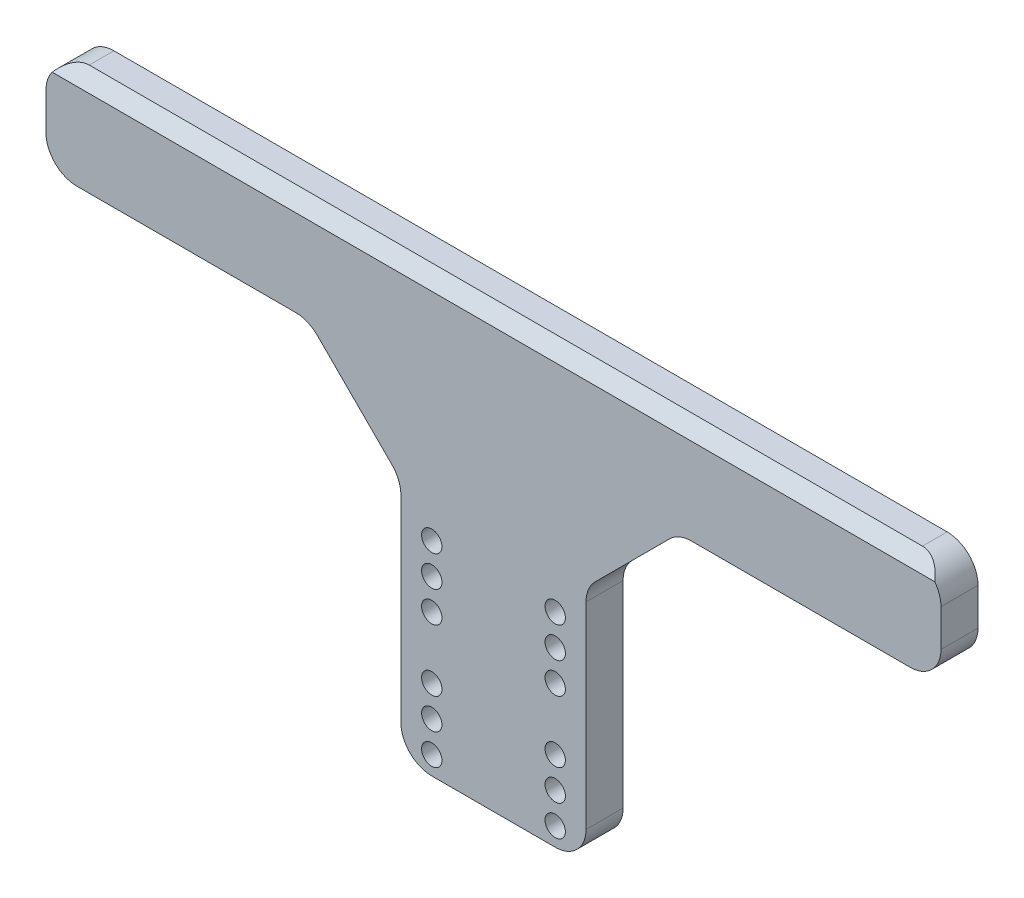
SolidWorks part; units mm, degrees
ref_plane "Front" through (0, 0, 0) normal (0, 0, 1) x (1, 0, 0)
ref_plane "Top" through (0, 0, 0) normal (0, 1, 0) x (1, 0, 0)
ref_plane "Right" through (0, 0, 0) normal (1, 0, 0) x (0, 0, -1)
sketch "Esquisse1" plane through (0, 0, 0) normal (0, 0, 1) x (1, 0, 0)
  line L1 (0, 0) -> (145, 0)
  line L2 (0, 0) -> (0, 40)
  line L3 (0, 40) -> (145, 40)
  line L4 (145, 0) -> (145, 40)
  dimension "D1" = 145
  dimension "D2" = 40
extrude "Boss.-Extru.1" add sketch "Esquisse1" along normal blind 6
sketch "Esquisse2" plane through (0, 0, 6) normal (0, 0, 1) x (1, 0, 0)
  line L0 (72.5, 0) -> (72.5, 40) construction
  line L1 (0, 0) -> (145, 0) construction
  line L2 (145, 40) -> (0, 40) construction
  line L3 (72.5, 13) -> (26.2893, 13) construction
  line L4 (62.5, 3) -> (62.5, 8) construction
  circle A0 centre (62.5, 23) radius 1.65
  circle A1 centre (62.5, 3) radius 1.65
  circle A2 centre (82.5, 3) radius 1.65
  circle A3 centre (82.5, 23) radius 1.65
  circle A4 centre (62.5, 28) radius 1.65
  circle A5 centre (62.5, 8) radius 1.65
  circle A6 centre (82.5, 8) radius 1.65
  circle A7 centre (82.5, 28) radius 1.65
  circle A8 centre (62.5, 33) radius 1.65
  circle A9 centre (62.5, 13) radius 1.65
  circle A10 centre (82.5, 13) radius 1.65
  circle A11 centre (82.5, 33) radius 1.65
  dimension "D1" = 20
  dimension "D2" = 20
  dimension "D3" = 3.3
  dimension "D4" = 3
  dimension "D6" = 5
  dimension "D5" = 3
extrude "Enlèv. mat.-Extru.1" cut sketch "Esquisse2" against normal through all both and the other way through all
sketch "Esquisse3" plane through (0, 0, 6) normal (0, 0, 1) x (1, 0, 0)
  line L0 (145, 0) -> (145, 40) construction
  line L1 (0, 40) -> (145, 40)
  line L2 (0, 40) -> (0, 70)
  line L3 (0, 70) -> (145, 70)
  line L4 (145, 40) -> (145, 70)
  dimension "D1" = 30
extrude "Boss.-Extru.2" add sketch "Esquisse3" against normal up to vertex (6 mm away)
chamfer "Chanfrein1" distance 2 angle 45 1 edges at (72.5, 70, 6)
sketch "Esquisse4" plane through (0, 0, 6) normal (0, 0, 1) x (1, 0, 0)
  line L0 (72.5, 0) -> (72.5, 70) construction
  line L1 (0, 0) -> (57.5, 0)
  line L2 (0, 0) -> (0, 54)
  line L3 (0, 54) -> (57.5, 54)
  line L4 (57.5, 0) -> (57.5, 54)
  line L5 (0, 0) -> (145, 0) construction
  line L6 (0, 70) -> (145, 70) construction
  line L7 (87.5, 0) -> (87.5, 54)
  line L8 (145, 54) -> (87.5, 54)
  line L9 (145, 0) -> (145, 54)
  line L10 (145, 0) -> (87.5, 0)
  dimension "D1" = 30
  dimension "D2" = 16
extrude "Enlèv. mat.-Extru.2" cut sketch "Esquisse4" against normal through all both and the other way through all
chamfer "Chanfrein2" distance 15 angle 45 2 edges at (87.5, 54, 3) (57.5, 54, 3)
fillet "Congé2" radius 5 10 edges at (145, 70, 2) (145, 54, 3) (102.5, 54, 3) (87.5, 39, 3) (87.5, 0, 3) (57.5, 0, 3) (57.5, 39, 3) (42.5, 54, 3) (0, 54, 3) (0, 70, 2)
